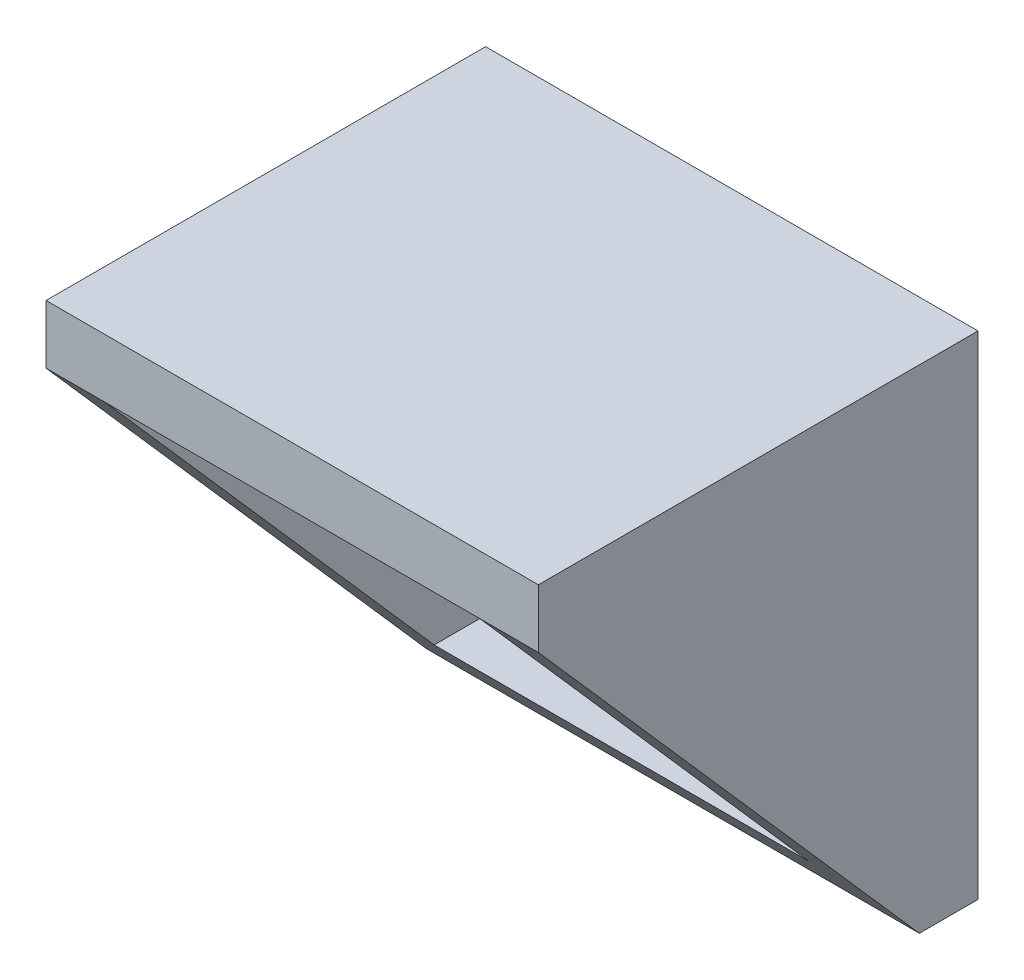
SolidWorks part; units mm, degrees
ref_plane "Front" through (0, 0, 0) normal (0, 0, 1) x (1, 0, 0)
ref_plane "Top" through (0, 0, 0) normal (0, 1, 0) x (1, 0, 0)
ref_plane "Right" through (0, 0, 0) normal (1, 0, 0) x (0, 0, -1)
sketch "Sketch1" plane through (0, 0, 0) normal (0, 0, 1) x (1, 0, 0)
  line L0 (0, 6.4) -> (0, -6.4) construction
  line L1 (-6.4, 6.4) -> (6.4, 6.4)
  line L2 (-6.4, 6.4) -> (-6.4, -6.4)
  line L3 (-6.4, -6.4) -> (6.4, -6.4)
  line L4 (6.4, 6.4) -> (6.4, -6.4)
  line L5 (-8.4, 8.4) -> (8.4, 8.4)
  line L6 (-8.4, 8.4) -> (-8.4, -8.4)
  line L7 (-8.4, -8.4) -> (8.4, -8.4)
  line L8 (8.4, 8.4) -> (8.4, -8.4)
  line L9 (6.4, 0) -> (-6.4, 0) construction
  line L10 (0, -50) -> (0, 50) construction
  line L11 (50, 0) -> (-50, 0) construction
  point P17 (0, 8.4)
  point P18 (8.4, 0)
  dimension "D1" = 12.8
  dimension "D2" = 12.8
  dimension "D3" = 2
  dimension "D4" = 2
extrude "Boss-Extrude1" add sketch "Sketch1" along normal blind 15
sketch "Sketch2" plane through (8.4, 0, 0) normal (1, 0, 0) x (0, 0, -1)
  line L0 (-15, 6.4) -> (-2, -8.4)
  line L1 (-2, -8.4) -> (-15, -8.4)
  line L3 (-15, 6.4) -> (0, 6.4) construction
  line L4 (-15, -8.4) -> (0, -8.4) construction
  line L5 (-15, 6.4) -> (-15, -8.4)
  line L6 (-15, -8.4) -> (-15, 8.4) construction
  line L7 (0, -8.4) -> (0, 8.4) construction
  dimension "D2" = 2
extrude "Cut-Extrude1" cut sketch "Sketch2" against normal through all
equation "\"D2@Sketch1\"=\"D1@Sketch1\""
equation "\"D4@Sketch1\"=\"D3@Sketch1\""
